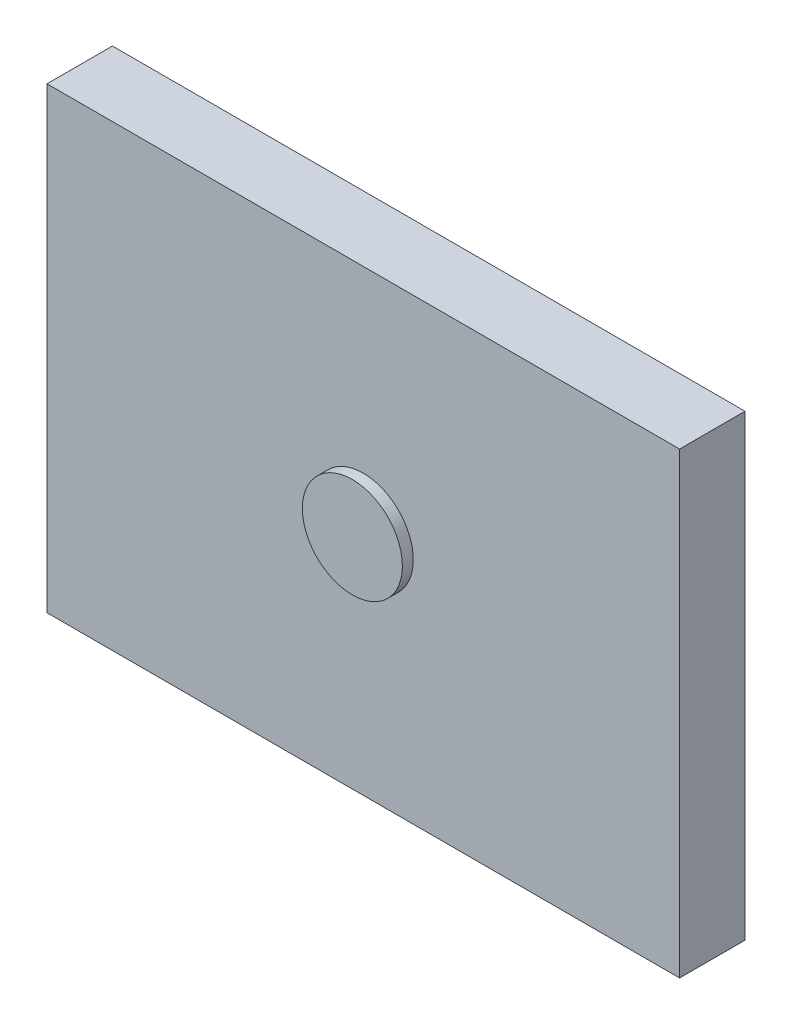
SolidWorks part; units mm, degrees
ref_plane "前视基准面" through (0, 0, 0) normal (0, 0, 1) x (1, 0, 0)
ref_plane "上视基准面" through (0, 0, 0) normal (0, 1, 0) x (1, 0, 0)
ref_plane "右视基准面" through (0, 0, 0) normal (1, 0, 0) x (0, 0, -1)
sketch "草图1" plane through (0, 0, 0) normal (0, 0, 1) x (1, 0, 0)
  line L1 (-145, -105) -> (145, -105)
  line L2 (-145, -105) -> (-145, 105)
  line L3 (-145, 105) -> (145, 105)
  line L4 (145, -105) -> (145, 105)
  line L5 (-145, -105) -> (145, 105) construction
  line L6 (-145, 105) -> (145, -105) construction
  point P0 (0, 0)
  dimension "D1" = 290
  dimension "D2" = 210
extrude "凸台-拉伸1" add sketch "草图1" along normal blind 30
sketch "草图2" plane through (0, 0, 30) normal (0, 0, 1) x (1, 0, 0)
  circle A0 centre (0, 0) radius 22.9203
extrude "凸台-拉伸2" add sketch "草图2" along normal blind 5
